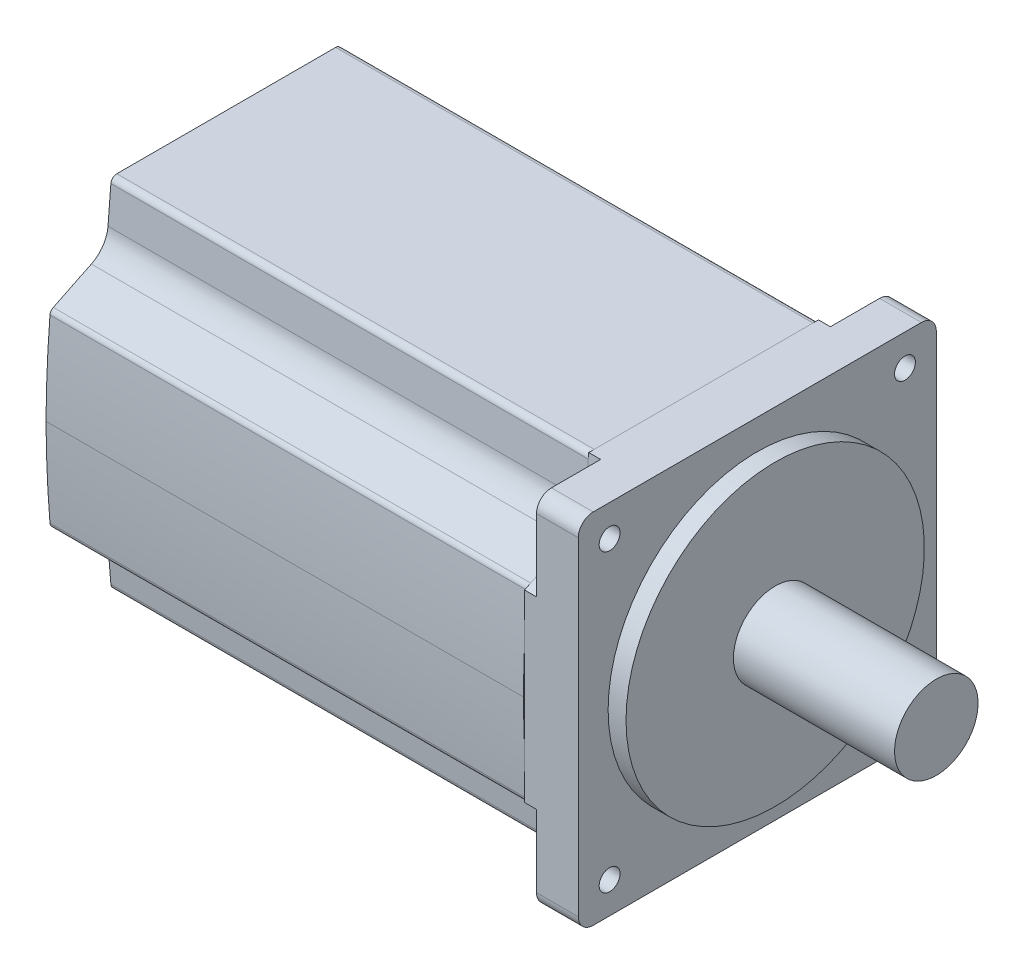
SolidWorks part; units mm, degrees
ref_plane "Front" through (0, 0, 0) normal (0, 0, 1) x (1, 0, 0)
ref_plane "Top" through (0, 0, 0) normal (0, 1, 0) x (1, 0, 0)
ref_plane "Right" through (0, 0, 0) normal (1, 0, 0) x (0, 0, -1)
sketch "Sketch7" plane through (0, 0, 0) normal (1, 0, 0) x (0, 0, -1)
  line L0 (-18.3326, -30) -> (18.3326, -30)
  line L1 (-22.6017, -19.0312) -> (-28.9769, -15.9218)
  line L2 (19.8097, -23.1233) -> (19.3294, -29.0804)
  line L3 (22.6017, -19.0312) -> (28.9769, -15.9218)
  line L4 (-19.8097, 23.1233) -> (-19.3294, 29.0804)
  line L5 (22.6017, 19.0312) -> (28.9769, 15.9218)
  line L6 (19.8097, 23.1233) -> (19.3294, 29.0804)
  line L7 (-19.8097, -23.1233) -> (-19.3294, -29.0804)
  line L8 (-22.6017, 19.0312) -> (-28.9769, 15.9218)
  line L9 (-18.3326, 30) -> (18.3326, 30)
  line L10 (0, 32.2863) -> (0, -37.493) construction
  line L11 (-32.8793, 0) -> (34.8831, 0) construction
  arc A0 (19.8097, -23.1233) -> (22.6017, -19.0312) centre (24.7936, -23.5252) cw
  arc A1 (29.5352, -15.1047) -> (28.9769, -15.9218) centre (28.5385, -15.023) cw
  arc A2 (-19.3294, -29.0804) -> (-18.3326, -30) centre (-18.3326, -29) ccw
  arc A3 (30.2002, 0) -> (29.5352, -15.1047) centre (-169.9959, 1.2475) cw
  arc A4 (-30.2002, 0) -> (-29.5352, -15.1047) centre (169.9959, 1.2475) ccw
  arc A5 (-29.5352, -15.1047) -> (-28.9769, -15.9218) centre (-28.5385, -15.023) ccw
  arc A6 (19.3294, -29.0804) -> (18.3326, -30) centre (18.3326, -29) cw
  arc A7 (-19.8097, 23.1233) -> (-22.6017, 19.0312) centre (-24.7936, 23.5252) cw
  arc A8 (19.3294, 29.0804) -> (18.3326, 30) centre (18.3326, 29) ccw
  arc A9 (-29.5352, 15.1047) -> (-28.9769, 15.9218) centre (-28.5385, 15.023) cw
  arc A10 (-30.2002, 0) -> (-29.5352, 15.1047) centre (169.9959, -1.2475) cw
  arc A11 (30.2002, 0) -> (29.5352, 15.1047) centre (-169.9959, -1.2475) ccw
  arc A12 (-19.3294, 29.0804) -> (-18.3326, 30) centre (-18.3326, 29) cw
  arc A13 (29.5352, 15.1047) -> (28.9769, 15.9218) centre (28.5385, 15.023) ccw
  arc A14 (-19.8097, -23.1233) -> (-22.6017, -19.0312) centre (-24.7936, -23.5252) ccw
  arc A15 (19.8097, 23.1233) -> (22.6017, 19.0312) centre (24.7936, 23.5252) ccw
  dimension "D2" = 1
  dimension "D5" = 5
  dimension "D6" = 1
  dimension "D7" = 200.2
  dimension "D1" = 60.4005
  dimension "D3" = 30
  dimension "D4" = 36.6652
  dimension "D8" = 7.0931
  dimension "D9" = 5.9571
  dimension "D11" = 94.61
  dimension "D12" = 26
extrude "Boss-Extrude3" add sketch "Sketch7" against normal blind 80
sketch "Sketch9" plane through (0, 0, 0) normal (1, 0, 0) x (0, 0, -1)
  line L0 (0, 40.7401) -> (0, -39.2496) construction
  line L1 (-30, 30) -> (30, 30)
  line L2 (-30, 30) -> (-30, -30)
  line L3 (-30, -30) -> (30, -30)
  line L4 (30, 30) -> (30, -30)
  dimension "D1" = 60
  dimension "D2" = 60
  dimension "D3" = 30
extrude "Boss-Extrude4" add sketch "Sketch9" along normal blind 9 separate body
sketch "Sketch8" plane through (0, 0, 0) normal (0, 0, 1) x (1, 0, 0)
  line L0 (-4.8998, 0) -> (42.4854, 0) construction
  line L1 (39, 0) -> (39, 7)
  line L2 (39, 7) -> (12, 7)
  line L3 (12, 7) -> (12, 25)
  line L4 (12, 25) -> (9, 25)
  line L5 (9, 25) -> (9, 0)
  line L6 (9, 0) -> (39, 0)
  line L8 (9, 30) -> (9, -30) construction
  dimension "D1" = 3
  dimension "D2" = 27
  dimension "D3" = 14
  dimension "D4" = 50
revolve "Revolve5" add sketch "Sketch8" angle 360 about L0
sketch "Sketch12" plane through (0, 0, 0) normal (-1, 0, 0) x (0, 0, 1)
  line L0 (-28.9769, 15.9218) -> (-22.6017, 19.0312) construction
  line L1 (-19.8097, 23.1233) -> (-19.3294, 29.0804) construction
  line L2 (19.3294, 29.0804) -> (19.8097, 23.1233) construction
  line L3 (22.6017, 19.0312) -> (28.9769, 15.9218) construction
  line L4 (-22.6017, -19.0312) -> (-28.9769, -15.9218) construction
  line L5 (-19.3294, -29.0804) -> (-19.8097, -23.1233) construction
  line L6 (19.8097, -23.1233) -> (19.3294, -29.0804) construction
  line L7 (28.9769, -15.9218) -> (22.6017, -19.0312) construction
  line L8 (-28.9769, 15.9218) -> (-22.6017, 19.0312)
  line L9 (-19.8097, 23.1233) -> (-19.3294, 29.0804)
  line L10 (19.3294, 29.0804) -> (19.8097, 23.1233)
  line L11 (22.6017, 19.0312) -> (28.9769, 15.9218)
  line L12 (-22.6017, -19.0312) -> (-28.9769, -15.9218)
  line L13 (-19.3294, -29.0804) -> (-19.8097, -23.1233)
  line L14 (19.8097, -23.1233) -> (19.3294, -29.0804)
  line L15 (28.9769, -15.9218) -> (22.6017, -19.0312)
  line L16 (-28.9769, 15.9218) -> (-30, 15.4228)
  line L17 (-19.3294, 29.0804) -> (-19.2552, 30)
  line L18 (-30, 30) -> (-30, 15.4228)
  line L19 (-30, -30) -> (-30, 30) construction
  line L20 (-30, 30) -> (-19.2552, 30)
  line L21 (-30, 30) -> (30, 30) construction
  line L22 (19.3294, 29.0804) -> (19.2552, 30)
  line L23 (28.9769, 15.9218) -> (30, 15.4228)
  line L24 (30, 30) -> (30, 15.4228)
  line L26 (30, 30) -> (30, -30) construction
  line L27 (30, 30) -> (19.2552, 30)
  line L28 (19.3294, -29.0804) -> (19.2552, -30)
  line L29 (28.9769, -15.9218) -> (30, -15.4228)
  line L30 (30, -30) -> (30, -15.4228)
  line L31 (30, -30) -> (19.2552, -30)
  line L33 (30, -30) -> (-30, -30) construction
  line L34 (-19.3294, -29.0804) -> (-19.2552, -30)
  line L35 (-28.9769, -15.9218) -> (-30, -15.4228)
  line L36 (-30, -30) -> (-19.2552, -30)
  line L37 (-30, -30) -> (-30, -15.4228)
  arc A0 (-22.6017, 19.0312) -> (-19.8097, 23.1233) centre (-24.7936, 23.5252) ccw construction
  arc A1 (19.8097, 23.1233) -> (22.6017, 19.0312) centre (24.7936, 23.5252) ccw construction
  arc A2 (-19.8097, -23.1233) -> (-22.6017, -19.0312) centre (-24.7936, -23.5252) ccw construction
  arc A3 (22.6017, -19.0312) -> (19.8097, -23.1233) centre (24.7936, -23.5252) ccw construction
  arc A4 (-22.6017, 19.0312) -> (-19.8097, 23.1233) centre (-24.7936, 23.5252) ccw
  arc A5 (19.8097, 23.1233) -> (22.6017, 19.0312) centre (24.7936, 23.5252) ccw
  arc A6 (-19.8097, -23.1233) -> (-22.6017, -19.0312) centre (-24.7936, -23.5252) ccw
  arc A7 (22.6017, -19.0312) -> (19.8097, -23.1233) centre (24.7936, -23.5252) ccw
extrude "Cut-Extrude1" cut sketch "Sketch12" against normal blind 2
hole_wizard "Ø3.5 (3.5) Diameter Hole1" positions "Sketch11" profile "Sketch10" hole size "Ø3.5" standard "JIS" end condition up to next
sketch "Sketch11" plane through (9, 0, 0) normal (1, 0, 0) x (0, 0, -1)
  line L0 (26.9437, 26.9437) -> (-31.1834, -31.1834) construction
  line L1 (-30.4063, 30.4063) -> (30.7428, -30.7428) construction
  line L2 (-40.7673, 0) -> (40.4553, 0) construction
  circle A0 centre (0, 0) radius 35 construction
  point P0 (-24.7487, 24.7487)
  point P18 (24.7487, 24.7487)
  point P22 (-24.7487, -24.7487)
  point P26 (24.7487, -24.7487)
  dimension "D1" = 70
  dimension "D2" = 45
sketch "Sketch10" plane through (9, 24.7487, 24.7487) normal (0, 1, 0) x (0, 0, -1)
  line L0 (0, 0) -> (0, 7)
  line L1 (0, 7) -> (1.75, 7)
  line L2 (1.75, 7) -> (1.75, 0)
  line L5 (1.75, 0) -> (0, 0)
  line L11 (0, -6.35) -> (0, 107.95) construction
  dimension "Thru Hole Dia." = 3.5
  dimension "Thru Hole Depth" = 7
fillet "Fillet2" radius 2.5 4 edges at (5.5, -30, -30) (5.5, -30, 30) (5.5, 30, -30) (5.5, 30, 30)
